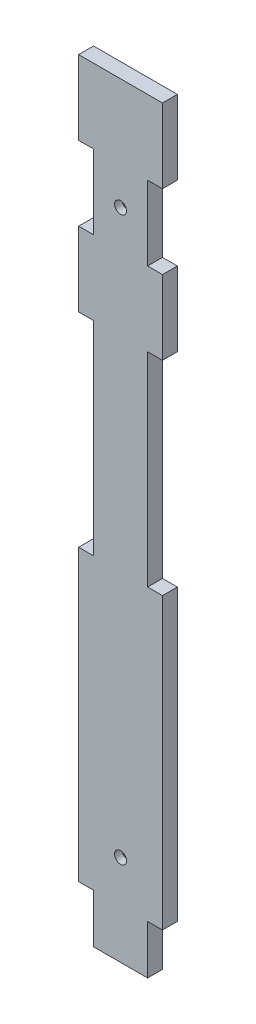
SolidWorks part; units mm, degrees
ref_plane "Front Plane" through (0, 0, 0) normal (0, 0, 1) x (1, 0, 0)
ref_plane "Top Plane" through (0, 0, 0) normal (0, 1, 0) x (1, 0, 0)
ref_plane "Right Plane" through (0, 0, 0) normal (1, 0, 0) x (0, 0, -1)
sketch "Sketch1" plane through (0, 0, 0) normal (0, 0, 1) x (1, 0, 0)
  line L0 (0, 150) -> (56.4, 150)
  line L1 (0, 0) -> (56.4, 0) construction
  line L2 (0, 0) -> (0, 150) construction
  line L3 (0, 150) -> (56.4, 150) construction
  line L4 (56.4, 0) -> (56.4, 150) construction
  line L5 (56.4, 150) -> (56.4, 100)
  line L6 (56.4, 100) -> (46.4, 100)
  line L7 (46.4, 100) -> (46.4, 50)
  line L8 (46.4, 50) -> (56.4, 50)
  line L9 (56.4, 50) -> (56.4, 0)
  line L10 (56.4, 0) -> (0, 0) construction
  line L11 (28.2, 150) -> (28.2, 0) construction
  line L12 (0, 150) -> (0, 100)
  line L13 (0, 50) -> (0, 0)
  line L14 (10, 50) -> (0, 50)
  line L15 (10, 100) -> (10, 50)
  line L16 (0, 100) -> (10, 100)
  line L17 (0, -137.1275) -> (0, -332.0213)
  line L18 (0, -332.0213) -> (10, -332.0213)
  line L19 (10, -332.0213) -> (10, -365)
  line L20 (10, -365) -> (46.4, -365)
  line L21 (46.4, -365) -> (46.4, -332.0213)
  line L22 (46.4, -332.0213) -> (56.4, -332.0213)
  line L23 (56.4, -332.0213) -> (56.4, -137.1275)
  line L25 (56.4, 0) -> (46.4, 0)
  line L26 (46.4, 0) -> (46.4, -137.1275)
  line L27 (46.4, -137.1275) -> (56.4, -137.1275)
  line L28 (0, -137.1275) -> (10, -137.1275)
  line L29 (10, -137.1275) -> (10, 0)
  line L30 (10, 0) -> (0, 0)
  circle A0 centre (28.2, 75) radius 4
  circle A1 centre (28.2, -303.8213) radius 4
  circle A3 centre (28.2, -303.8213) radius 4 construction
  dimension "D6" = 8
  dimension "D1" = 56.4
  dimension "D2" = 150
  dimension "D3" = 50
  dimension "D4" = 50
  dimension "D5" = 10
extrude "Boss-Extrude1" add sketch "Sketch1" along normal blind 10
chamfer "Chamfer1" distance 5 angle 45 2 edges at (32.2, 75, 0) (32.2, -303.8213, 0)
